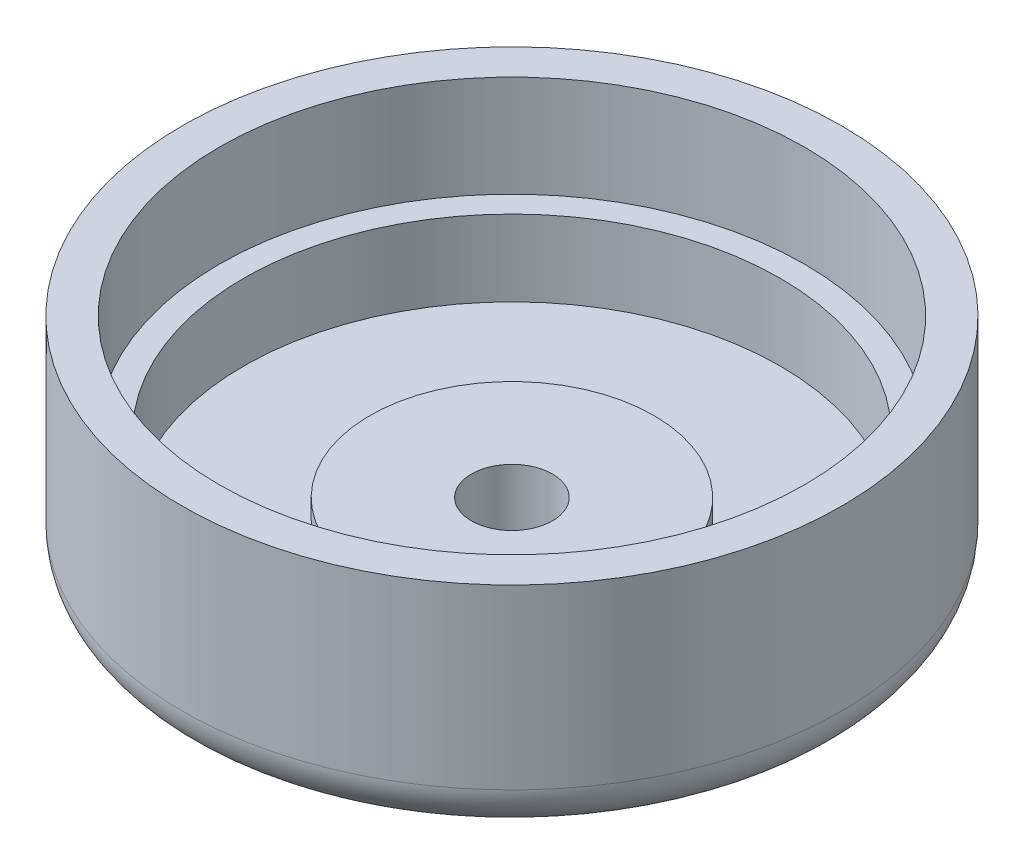
SolidWorks part; units mm, degrees
ref_plane "Front Plane" through (0, 0, 0) normal (0, 0, 1) x (1, 0, 0)
ref_plane "Top Plane" through (0, 0, 0) normal (0, 1, 0) x (1, 0, 0)
ref_plane "Right Plane" through (0, 0, 0) normal (1, 0, 0) x (0, 0, -1)
sketch "Sketch2" plane through (0, 0, 0) normal (0, 0, 1) x (1, 0, 0)
  line L0 (0, 0) -> (0, 78912.8151) construction
  line L2 (4, 0) -> (28.5227, 0)
  line L3 (4, 0) -> (4, 4)
  line L4 (14, 4.5) -> (26.45, 4.5)
  line L8 (28.85, 12) -> (26.45, 12)
  line L9 (26.45, 4.5) -> (26.45, 12)
  line L10 (28.5227, 0) -> (32.5, 0)
  line L13 (32.5, 0) -> (32.5, 10)
  line L15 (32.5, 10) -> (32.5, 22)
  line L16 (32.5, 22) -> (28.85, 22)
  line L17 (28.85, 12) -> (28.85, 22)
  line L19 (4, 4) -> (4, 6.5)
  line L20 (4, 6.5) -> (14, 6.5)
  line L21 (14, 4.5) -> (14, 6.5)
  dimension "D1" = 10
  dimension "D2" = 52.9
  dimension "D3" = 57.7
  dimension "D4" = 7.5
  dimension "D5" = 65
  dimension "D6" = 4.5
  dimension "D7" = 8
  dimension "D8" = 28
  dimension "D9" = 2
revolve "Revolve1" add sketch "Sketch2" angle 360 about L0
fillet "Fillet1" radius 4.5 1 edges at (0, 0, -32.5)
